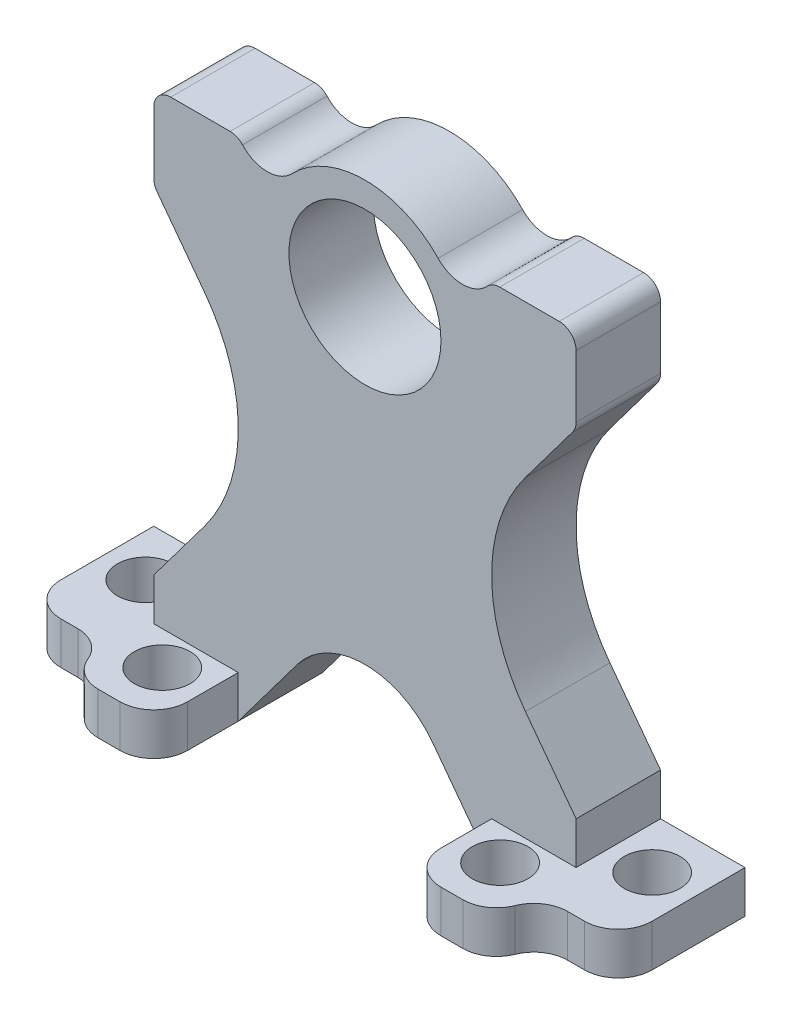
SolidWorks part; units mm, degrees
ref_plane "Front Plane" through (0, 0, 0) normal (0, 0, 1) x (1, 0, 0)
ref_plane "Top Plane" through (0, 0, 0) normal (0, 1, 0) x (1, 0, 0)
ref_plane "Right Plane" through (0, 0, 0) normal (1, 0, 0) x (0, 0, -1)
sketch "Sketch1" plane through (0, 0, 0) normal (0, 0, 1) x (1, 0, 0)
  line L0 (-7.5, 15) -> (-5.6466, 12.5288)
  line L1 (-12.5, -15) -> (-7.5, -15)
  line L2 (-12.5, -15) -> (-12.5, -10)
  line L3 (-12.5, 15) -> (-7.5, 15)
  line L4 (12.5, -15) -> (12.5, -10)
  line L5 (7.5, -15) -> (12.5, -15)
  line L6 (-12.5, 10) -> (-12.5, 15)
  line L7 (5.6466, 12.5288) -> (7.5, 15)
  line L8 (12.5, 15) -> (12.5, 10)
  line L9 (12.5, -10) -> (5, 0)
  line L10 (5, 0) -> (12.5, 10)
  line L11 (7.5, 15) -> (12.5, 15)
  line L12 (7.5, -15) -> (0, -5)
  line L13 (0, -5) -> (-7.5, -15)
  line L15 (-12.5, -10) -> (-5, 0)
  line L16 (-5, 0) -> (-12.5, 10)
  circle A0 centre (0, 10.5) radius 4.5
  arc A1 (5.6466, 12.5288) -> (-5.6466, 12.5288) centre (0, 10.5) ccw
  point P0 (0, 0)
  dimension "D2" = 30
  dimension "D3" = 25.5
  dimension "D4" = 5
  dimension "D1" = 25
  dimension "D5" = 5
  dimension "D6" = 5
  dimension "D7" = 5
  dimension "D8" = 5
  dimension "D9" = 5
  dimension "D10" = 5
  dimension "D11" = 0
  dimension "D12" = 5
  dimension "D16" = 5
  dimension "D17" = 5
  dimension "D18" = 0
  dimension "D19" = 5
extrude "Boss-Extrude1" add sketch "Sketch1" along normal blind 5
sketch "Sketch2" plane through (0, 0, 5) normal (0, 0, 1) x (1, 0, 0)
  line L0 (-12.5, -10) -> (-12.5, -15) construction
  line L1 (-7.5, -15) -> (-12.5, -15)
  line L2 (-7.5, -15) -> (-7.5, -12.5)
  line L3 (-7.5, -12.5) -> (-12.5, -12.5)
  line L4 (-12.5, -15) -> (-12.5, -12.5)
  line L5 (12.5, -15) -> (12.5, -10) construction
  line L6 (7.5, -15) -> (12.5, -15)
  line L7 (7.5, -15) -> (7.5, -12.5)
  line L8 (7.5, -12.5) -> (12.5, -12.5)
  line L9 (12.5, -15) -> (12.5, -12.5)
extrude "Boss-Extrude2" add sketch "Sketch2" along normal blind 5
sketch "Sketch3" plane through (12.5, 0, 0) normal (1, 0, 0) x (0, 0, -1)
  line L0 (-10, -12.5) -> (-5, -12.5) construction
  line L1 (0, -15) -> (-7.5, -15)
  line L2 (0, -15) -> (0, -12.5)
  line L3 (0, -12.5) -> (-7.5, -12.5)
  line L4 (-7.5, -15) -> (-7.5, -12.5)
extrude "Boss-Extrude3" add sketch "Sketch3" along normal blind 5
sketch "Sketch4" plane through (-12.5, 0, 0) normal (-1, 0, 0) x (0, 0, 1)
  line L0 (10, -12.5) -> (5, -12.5) construction
  line L1 (0, -15) -> (7.5, -15)
  line L2 (0, -15) -> (0, -12.5)
  line L3 (0, -12.5) -> (7.5, -12.5)
  line L4 (7.5, -15) -> (7.5, -12.5)
extrude "Boss-Extrude4" add sketch "Sketch4" along normal blind 5
sketch "Sketch5" plane through (0, -12.5, 0) normal (0, 1, 0) x (1, 0, 0)
  line L0 (-17.5, 0) -> (-12.5, 0) construction
  line L1 (17.5, 0) -> (12.5, 0) construction
  line L2 (-7.5, -10) -> (-12.5, -10) construction
  circle A0 centre (-15, -3) radius 1.65
  circle A1 centre (15, -3) radius 1.65
  circle A2 centre (-10, -7) radius 1.65
  circle A3 centre (10, -7) radius 1.65
  point P2 (-15, 0)
  dimension "D1" = 3
  dimension "D2" = 3
  dimension "D3" = 3
extrude "Cut-Extrude1" cut sketch "Sketch5" against normal blind 5
fillet "Fillet1" radius 2 4 edges at (17.5, -13.75, 7.5) (12.5, -13.75, 7.5) (-12.5, -13.75, 7.5) (-17.5, -13.75, 7.5)
fillet "Fillet2" radius 2 4 edges at (12.5, -13.75, 10) (7.5, -13.75, 10) (-7.5, -13.75, 10) (-12.5, -13.75, 10)
fillet "Fillet3" radius 2 2 edges at (5.6466, 12.5288, 2.5) (-5.6466, 12.5288, 2.5)
fillet "Fillet4" radius 10 2 edges at (5, 0, 2.5) (-5, 0, 2.5)
fillet "Fillet5" radius 5 1 edges at (0, -5, 2.5)
fillet "Fillet6" radius 1 6 edges at (-12.5, 10, 2.5) (-12.5, 15, 2.5) (-7.5, 15, 2.5) (12.5, 10, 2.5) (7.5, 15, 2.5) (12.5, 15, 2.5)
